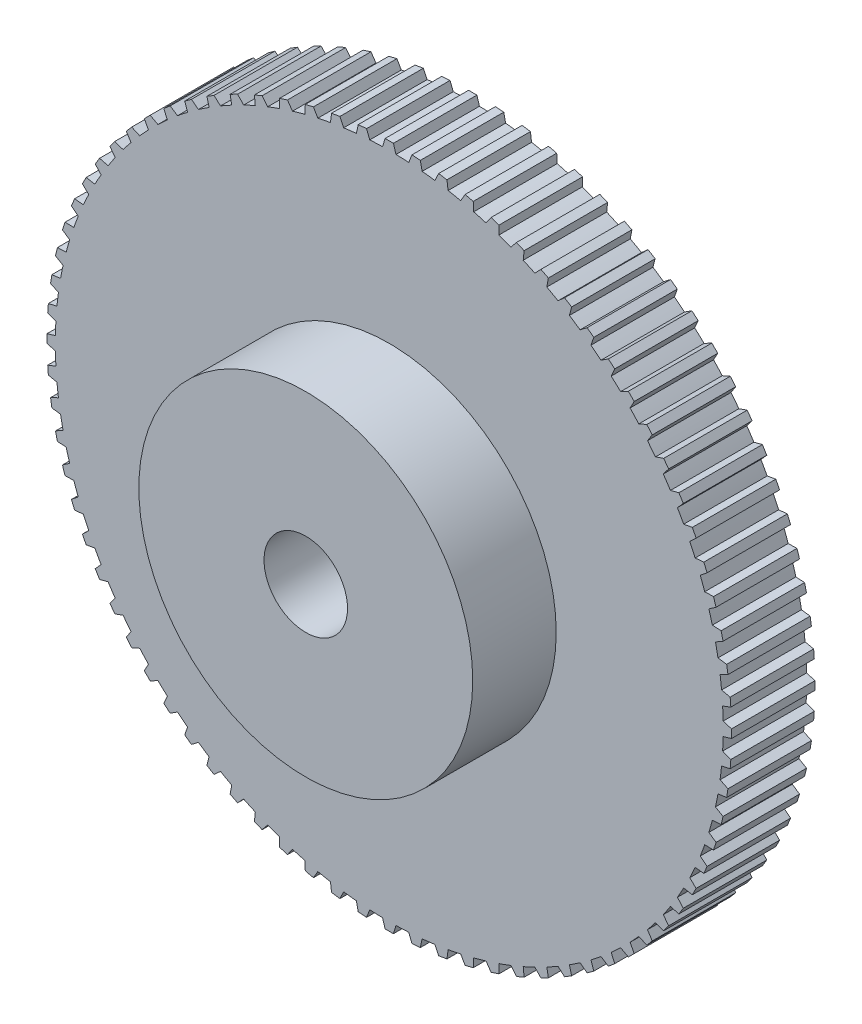
SolidWorks part; units mm, degrees
material "AISI 1045 鋼，冷拉"
ref_plane "前基準面" through (0, 0, 0) normal (0, 0, 1) x (1, 0, 0)
ref_plane "上基準面" through (0, 0, 0) normal (0, 1, 0) x (1, 0, 0)
ref_plane "右基準面" through (0, 0, 0) normal (1, 0, 0) x (0, 0, -1)
sketch "草圖1" plane through (0, 0, 0) normal (0, 0, 1) x (1, 0, 0)
  circle A0 centre (0, 0) radius 40
  dimension "D1" = 80
extrude "填料-伸長1" add sketch "草圖1" along normal blind 10
sketch "草圖2" plane through (0, 0, 10) normal (0, 0, 1) x (1, 0, 0)
  circle A0 centre (0, 0) radius 20
  dimension "D1" = 40
extrude "填料-伸長2" add sketch "草圖2" along normal blind 10
sketch "草圖3" plane through (0, 0, 20) normal (0, 0, 1) x (1, 0, 0)
  circle A0 centre (0, 0) radius 5
  dimension "D1" = 10
extrude "除料-伸長1" cut sketch "草圖3" against normal through all
sketch "草圖4" plane through (0, 0, 10) normal (0, 0, 1) x (1, 0, 0)
  line L0 (-2, 36) -> (2, 36)
  line L1 (2, 36) -> (0.5, 41)
  line L2 (0.5, 41) -> (-0.5, 41)
  line L3 (-0.5, 41) -> (-2, 36)
  line L4 (0, 0) -> (0, 41) construction
  circle A0 centre (0, 0) radius 40 construction
  point P7 (0, 36)
  dimension "D2" = 41
  dimension "D1" = 1
  dimension "D3" = 4
  dimension "D4" = 5
extrude "填料-伸長3" add sketch "草圖4" against normal blind 10
pattern_circular "環狀複製排列1" count 80 over 360 about axis through (0, 0, 0) along (0, 0, 1) of "填料-伸長3"
